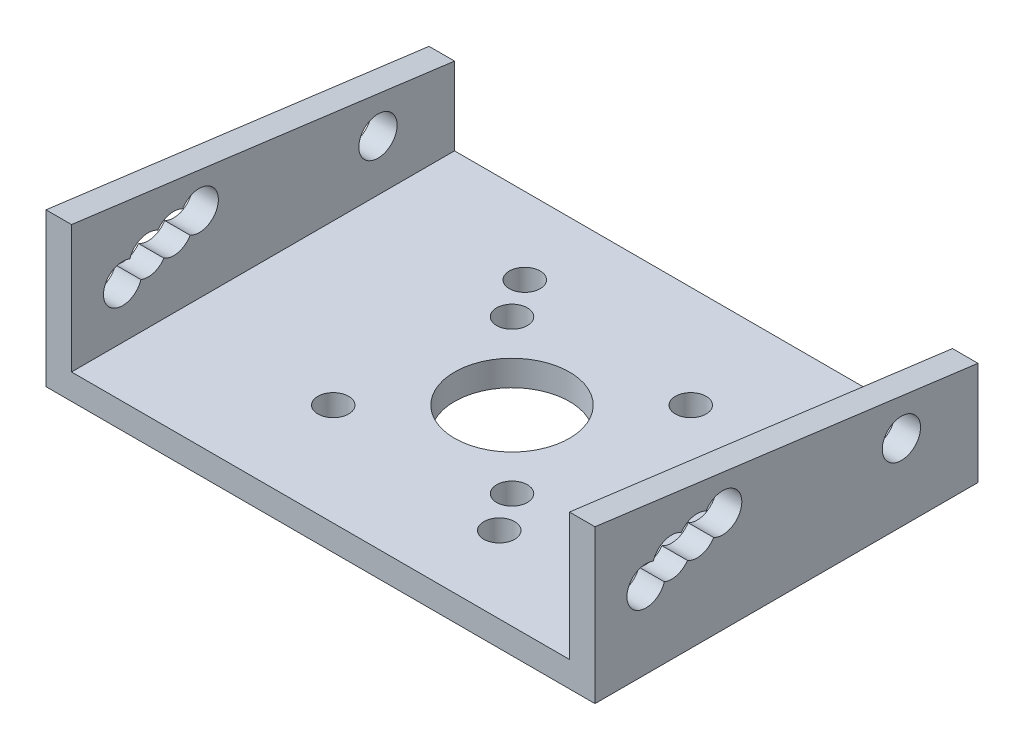
SolidWorks part; units mm, degrees
material "Náilon 6/10"
ref_plane "Plano frontal" through (0, 0, 0) normal (0, 0, 1) x (1, 0, 0)
ref_plane "Plano superior" through (0, 0, 0) normal (0, 1, 0) x (1, 0, 0)
ref_plane "Plano direito" through (0, 0, 0) normal (1, 0, 0) x (0, 0, -1)
sketch "Esboço1" plane through (0, 0, 0) normal (0, 1, 0) x (1, 0, 0)
  line L1 (-21.5, -15) -> (21.5, -15)
  line L2 (-21.5, -15) -> (-21.5, 15)
  line L3 (-21.5, 15) -> (21.5, 15)
  line L4 (21.5, -15) -> (21.5, 15)
  circle A0 centre (0, 0) radius 4.5
  circle A1 centre (7, 7) radius 1.2058
  circle A2 centre (-6, 6) radius 1.2058
  circle A3 centre (-8, 9) radius 1.2058
  circle A4 centre (-7, -7) radius 1.2058
  circle A5 centre (6, -6) radius 1.2058
  circle A6 centre (8, -9) radius 1.2058
  dimension "D3" = 9
  dimension "D1" = 43
  dimension "D2" = 30
  dimension "D4" = 7
  dimension "D5" = 7
  dimension "D6" = 6
  dimension "D7" = 6
  dimension "D8" = 8
  dimension "D9" = 9
  dimension "D10" = 7
  dimension "D11" = 7
  dimension "D12" = 6
  dimension "D13" = 6
  dimension "D14" = 9
  dimension "D15" = 8
extrude "Ressalto-extrusão1" add sketch "Esboço1" along normal blind 2
sketch "Esboço2" plane through (-21.5, 0, 0) normal (-1, 0, 0) x (0, 0, 1)
  line L0 (-9, 6) -> (9, 6) construction
  line L1 (15, 12) -> (15, 2)
  line L2 (-9, 6) -> (5, 7.95) construction
  line L3 (-15, 2) -> (-15, 8.0894)
  line L5 (-15, 2) -> (15, 2) construction
  line L6 (-15, 8.0894) -> (15, 12)
  circle A0 centre (-9, 6) radius 1.5
  circle A1 centre (9, 6.94) radius 1.5
  circle A2 centre (7, 7.39) radius 1.5
  circle A3 centre (5, 7.95) radius 1.5
  circle A4 centre (11, 6) radius 1.5
  dimension "D1" = 18
  dimension "D3" = 3
  dimension "D5" = 1.39
  dimension "D9" = 3
  dimension "D2" = 6
  dimension "D4" = 0.94
  dimension "D6" = 16
  dimension "D7" = 14
  dimension "D8" = 1.95
  dimension "D10" = 4
  dimension "D11" = 20
  dimension "D12" = 10
extrude "Ressalto-extrusão2" add sketch "Esboço2" against normal blind 2
mirror "Espelhar1" about plane through (0, 0, 0) normal (1, 0, 0) of "Ressalto-extrusão2"
